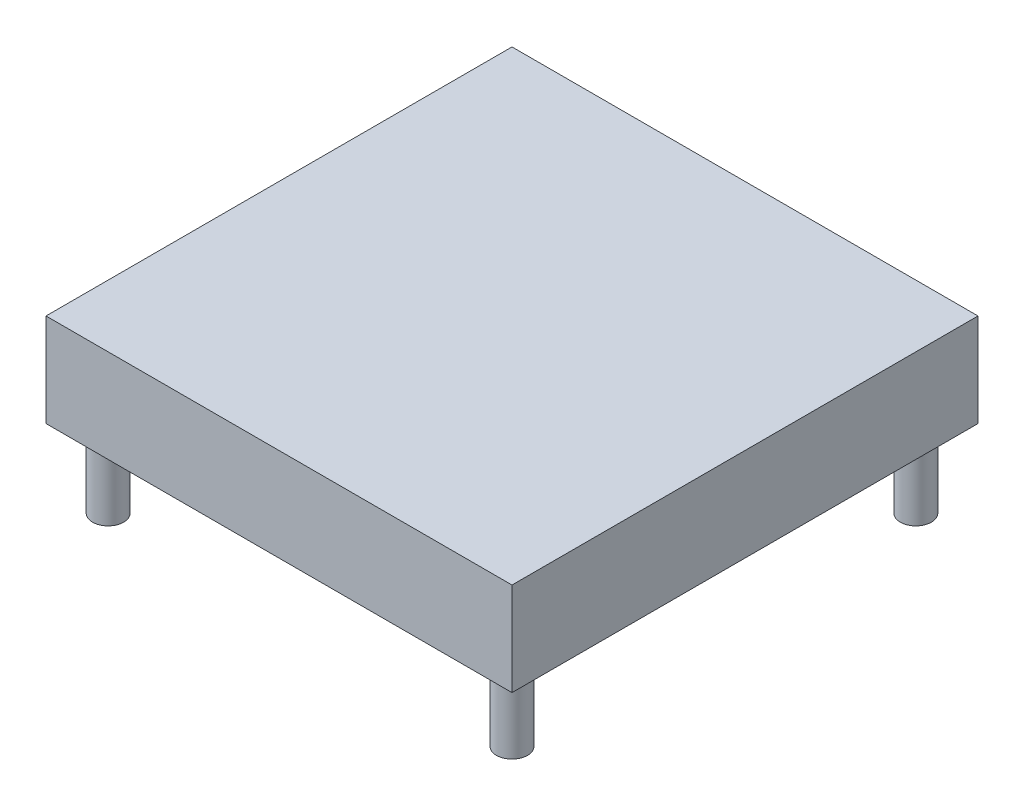
SolidWorks part; units mm, degrees
material "Custom Plastic"
ref_plane "Front Plane" through (0, 0, 0) normal (0, 0, 1) x (1, 0, 0)
ref_plane "Top Plane" through (0, 0, 0) normal (0, 1, 0) x (1, 0, 0)
ref_plane "Right Plane" through (0, 0, 0) normal (1, 0, 0) x (0, 0, -1)
sketch "Sketch1" plane through (0, 0, 0) normal (0, 1, 0) x (1, 0, 0)
  line L1 (-19.05, 19.05) -> (19.05, 19.05)
  line L2 (-19.05, 19.05) -> (-19.05, -19.05)
  line L3 (-19.05, -19.05) -> (19.05, -19.05)
  line L4 (19.05, 19.05) -> (19.05, -19.05)
  line L5 (-19.05, 19.05) -> (19.05, -19.05) construction
  line L6 (-19.05, -19.05) -> (19.05, 19.05) construction
  point P0 (0, 0)
extrude "Extrude1" add sketch "Sketch1" along normal blind 7.62
sketch "Sketch2" plane through (0, 0, 0) normal (0, -1, 0) x (1, 0, 0)
  line L0 (19.05, 19.05) -> (19.05, 16.51) construction
  line L1 (19.05, 19.05) -> (19.05, -19.05) construction
  line L2 (19.05, 16.51) -> (16.51, 16.51) construction
  line L3 (19.05, 0) -> (0, 0) construction
  line L4 (0, 19.05) -> (0, -19.05) construction
  line L5 (-19.05, 19.05) -> (19.05, 19.05) construction
  line L6 (19.05, -19.05) -> (-19.05, -19.05) construction
  circle A0 centre (16.51, 16.51) radius 1.27
  circle A1 centre (16.51, -16.51) radius 1.27
  circle A2 centre (-16.51, -16.51) radius 1.27
  circle A3 centre (-16.51, 16.51) radius 1.27
extrude "Extrude2" add sketch "Sketch2" along normal blind 6.35
